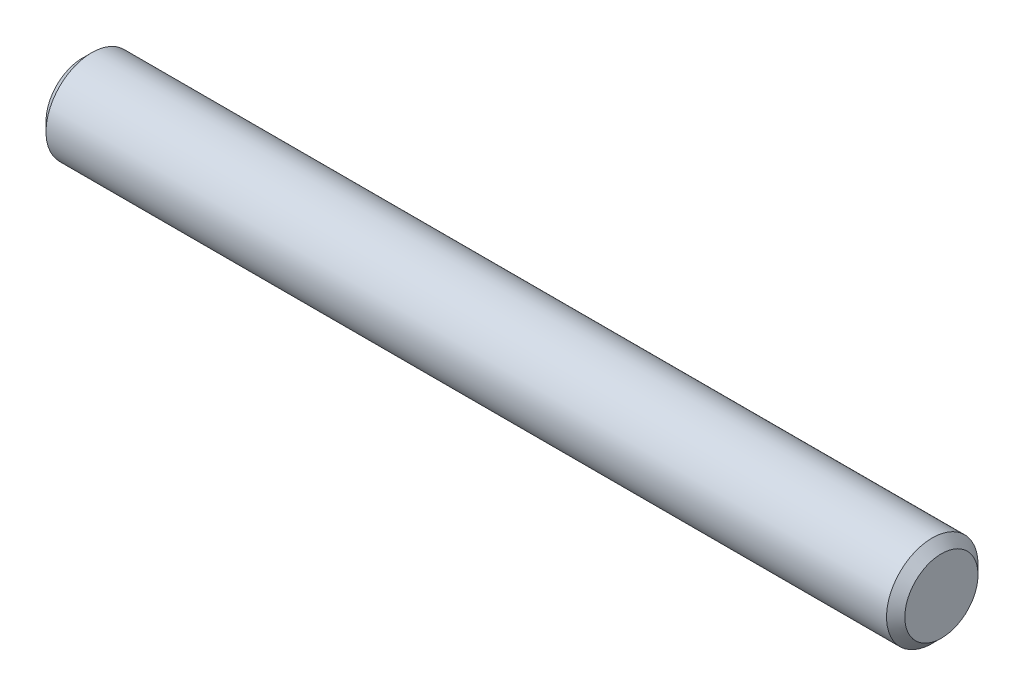
SolidWorks part; units mm, degrees
material "A-Glass Fiber"
ref_plane "Front" through (0, 0, 0) normal (0, 0, 1) x (1, 0, 0)
ref_plane "Top" through (0, 0, 0) normal (0, 1, 0) x (1, 0, 0)
ref_plane "Right" through (0, 0, 0) normal (1, 0, 0) x (0, 0, -1)
sketch "Sketch1" plane through (0, 0, 0) normal (0, 0, 1) x (1, 0, 0)
  line L0 (-5.588, 0) -> (5.588, 0) construction
  line L1 (5.588, 0.5953) -> (5.588, -0.5953) construction
  line L2 (-5.588, 0.5953) -> (-5.588, -0.5953) construction
  dimension "Length" = 11.176
  dimension "Diameter" = 1.1906
sketch "Sketch2" plane through (0, 0, 0) normal (1, 0, 0) x (0, 0, -1)
  circle A0 centre (0, 0) radius 0.5953
extrude "Extrude1" add sketch "Sketch2" against normal up to vertex (5.588 mm away) and the other way up to vertex (5.588 mm away) up to point (-5.588, 0.5953, 0) other way up to point (5.588, 0.5953, 0)
chamfer "Chamfer1" distance 0.1191 angle 45 2 edges at (5.588, 0, -0.5953) (-5.588, 0, -0.5953)
equation "\"D1@Chamfer1\" = \"Diameter@Sketch1\"*.1"
